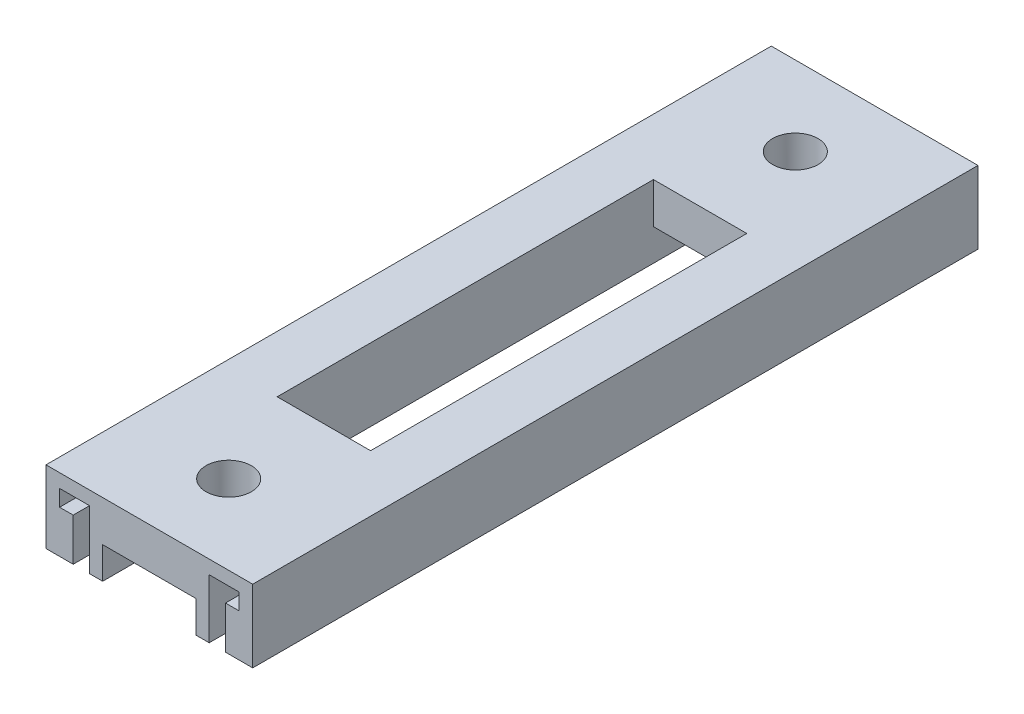
SolidWorks part; units mm, degrees
ref_plane "Front Plane" through (0, 0, 0) normal (0, 0, 1) x (1, 0, 0)
ref_plane "Top Plane" through (0, 0, 0) normal (0, 1, 0) x (1, 0, 0)
ref_plane "Right Plane" through (0, 0, 0) normal (1, 0, 0) x (0, 0, -1)
sketch "Sketch2" plane through (0, 0, 0) normal (0, 0, 1) x (1, 0, 0)
  line L0 (0, 0) -> (0, 9.4)
  line L1 (0, 9.4) -> (-3, 9.4)
  line L2 (-3, 9.4) -> (-3, 13)
  line L3 (-3, 13) -> (3.6, 13)
  line L4 (3.6, 13) -> (3.6, 0)
  line L5 (3.6, 0) -> (6.5, 0)
  line L6 (6.5, 0) -> (6.5, 16)
  line L7 (6.5, 16) -> (-6, 16)
  line L8 (-6, 16) -> (-6, 0)
  line L9 (-6, 0) -> (0, 0)
  line L10 (39.6, 0) -> (33.6, 0)
  line L11 (16.8, 0) -> (16.8, 16) construction
  line L12 (39.6, 16) -> (39.6, 0)
  line L13 (27.1, 16) -> (39.6, 16)
  line L14 (27.1, 0) -> (27.1, 16)
  line L15 (30, 0) -> (27.1, 0)
  line L16 (30, 13) -> (30, 0)
  line L17 (36.6, 13) -> (30, 13)
  line L18 (36.6, 9.4) -> (36.6, 13)
  line L19 (33.6, 9.4) -> (36.6, 9.4)
  line L20 (33.6, 0) -> (33.6, 9.4)
  dimension "D1" = 6
  dimension "D2" = 16
  dimension "D3" = 3.6
  dimension "D4" = 9.4
  dimension "D5" = 3
  dimension "D6" = 6.6
  dimension "D7" = 2.9
  dimension "D8" = 20.6
extrude "Boss-Extrude1" add sketch "Sketch2" along normal blind 160
sketch "Sketch3" plane through (0, 0, 0) normal (0, 1, 0) x (1, 0, 0)
  line L1 (6.5, 0) -> (27.1, 0)
  line L2 (6.5, 0) -> (6.5, -160)
  line L3 (6.5, -160) -> (27.1, -160)
  line L4 (27.1, 0) -> (27.1, -160)
extrude "Boss-Extrude2" add sketch "Sketch3" against normal blind 9 from surface at 16 starting at face at (0.25, 16, 80)
sketch "Sketch4" plane through (0, 0, 0) normal (0, 1, 0) x (1, 0, 0)
  line L0 (16.8, 0) -> (16.8, -17.5) construction
  line L1 (39.6, 0) -> (-6, 0) construction
  line L2 (-6, -80) -> (39.6, -80) construction
  line L3 (-6, -160) -> (-6, 0) construction
  line L4 (39.6, -160) -> (39.6, 0) construction
  circle A0 centre (16.8, -17.5) radius 5
  circle A1 centre (16.8, -142.5) radius 5
  dimension "D1" = 10
  dimension "D2" = 17.5
extrude "Cut-Extrude1" cut sketch "Sketch4" against normal up to surface (9 mm away) from surface at 16 up to face at (16.8, 7, 80) starting at face at (16.8, 16, 80)
sketch "Sketch5" plane through (0, 0, 0) normal (0, 1, 0) x (1, 0, 0)
  line L0 (-6, -80) -> (39.6, -80) construction
  line L1 (-6, -160) -> (-6, 0) construction
  line L2 (39.6, -160) -> (39.6, 0) construction
  line L6 (6.5, -38.5) -> (27.1, -38.5)
  line L7 (27.1, -38.5) -> (27.1, -121.5)
  line L8 (27.1, -121.5) -> (6.5, -121.5)
  line L9 (6.5, -38.5) -> (6.5, -121.5)
  point P9 (16.8, -80)
  dimension "D1" = 20.6
  dimension "D2" = 83
  dimension "D3" = 6.5
  dimension "D4" = 38.5
extrude "Cut-Extrude2" cut sketch "Sketch5" against normal up to surface (9 mm away) from surface at 16 up to face at (16.8, 7, 22.5) starting at face at (16.8, 16, 12.5)
